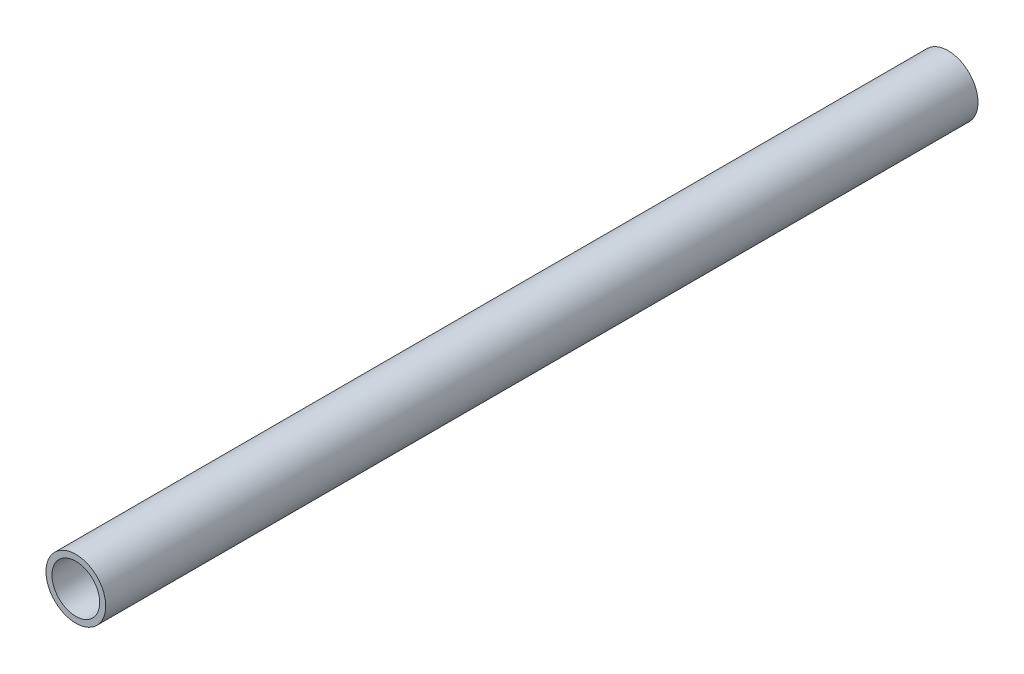
SolidWorks part; units mm, degrees
material "Thornel Mat VMA"
ref_plane "正面" through (0, 0, 0) normal (0, 0, 1) x (1, 0, 0)
ref_plane "平面" through (0, 0, 0) normal (0, 1, 0) x (1, 0, 0)
ref_plane "右側面" through (0, 0, 0) normal (1, 0, 0) x (0, 0, -1)
sketch "ｽｹｯﾁ1" plane through (0, 0, 0) normal (0, 0, 1) x (1, 0, 0)
  circle A0 centre (0, 0) radius 2.5
  circle A1 centre (0, 0) radius 2
  dimension "D1" = 5
  dimension "D2" = 0.5
extrude "ﾎﾞｽ - 押し出し1" add sketch "ｽｹｯﾁ1" along normal blind 73
